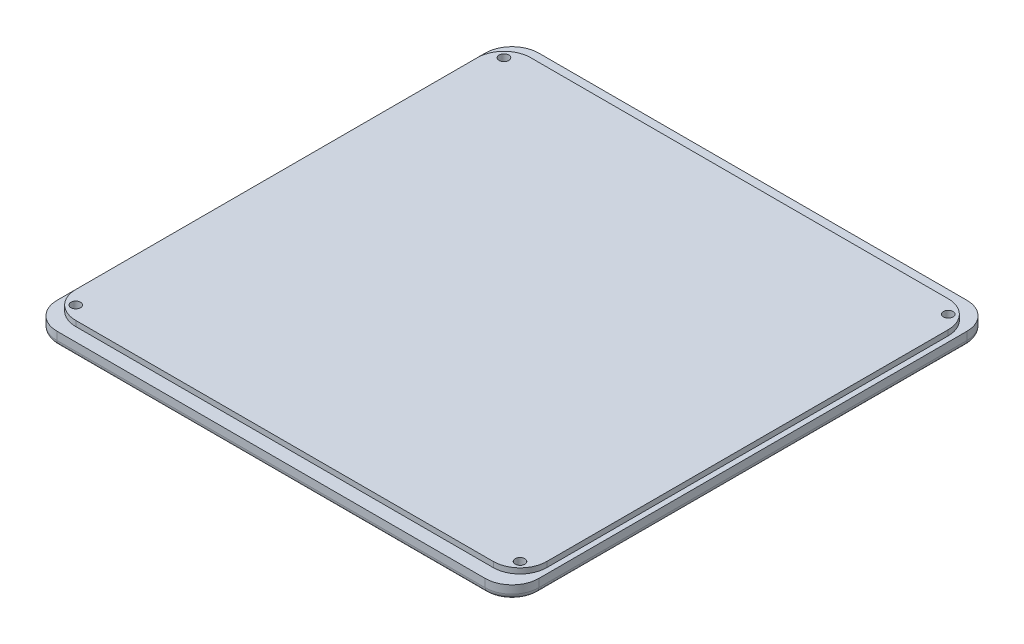
SolidWorks part; units mm, degrees
material "Allzweck-PBT"
ref_plane "Ebene vorne" through (0, 0, 0) normal (0, 0, 1) x (1, 0, 0)
ref_plane "Ebene oben" through (0, 0, 0) normal (0, 1, 0) x (1, 0, 0)
ref_plane "Ebene rechts" through (0, 0, 0) normal (1, 0, 0) x (0, 0, -1)
sketch "Skizze1" plane through (0, 0, 0) normal (0, 1, 0) x (1, 0, 0)
  line L1 (90, 90) -> (-90, 90)
  line L2 (90, 90) -> (90, -90)
  line L3 (90, -90) -> (-90, -90)
  line L4 (-90, 90) -> (-90, -90)
  line L5 (90, 90) -> (-90, -90) construction
  line L6 (90, -90) -> (-90, 90) construction
  point P0 (0, 0)
  dimension "D1" = 180
  dimension "D2" = 180
extrude "Aufsatz-Linear austragen1" add sketch "Skizze1" along normal blind 5 contours L4 L3 L2 L1
sketch "Skizze2" plane through (0, 5, 0) normal (0, 1, 0) x (1, 0, 0)
  line L1 (78, 85) -> (-78, 85)
  line L2 (88, 75) -> (88, -75)
  line L3 (78, -85) -> (-78, -85)
  line L4 (-88, 75) -> (-88, -75)
  line L5 (88, 85) -> (-88, -85) construction
  line L6 (88, -85) -> (-88, 85) construction
  arc A0 (-78, -85) -> (-88, -75) centre (-78, -75) cw
  arc A1 (88, -75) -> (78, -85) centre (78, -75) cw
  arc A2 (78, 85) -> (88, 75) centre (78, 75) cw
  arc A3 (-78, 85) -> (-88, 75) centre (-78, 75) ccw
  point P0 (0, 0)
  dimension "D1" = 10
  dimension "176" = 176
  dimension "D2" = 170
extrude "Aufsatz-Linear austragen2" add sketch "Skizze2" along normal blind 2
hole_wizard "Stirnsenkung für M3 Zylinderschraube mit Innensechskant2" positions "Skizze7" profile "Skizze8" counterbore size "M3" standard "DIN"
sketch "Skizze7" plane through (0, 0, 0) normal (0, -1, 0) x (-1, 0, 0)
  line L0 (-78, 85) -> (78, 85) construction
  line L1 (-88, -75) -> (-88, 75) construction
  line L2 (-78, 85) -> (78, 85) construction
  line L3 (88, 75) -> (88, -75) construction
  line L4 (78, -85) -> (-78, -85) construction
  point P0 (-83, 80)
  point P2 (83, 80)
  point P4 (83, -80)
  point P6 (-83, -80)
  dimension "D1" = 5
  dimension "D2" = 5
  dimension "D3" = 5
  dimension "D4" = 5
  dimension "D5" = 5
  dimension "D6" = 5
  dimension "D7" = 5
  dimension "5" = 5
sketch "Skizze8" plane through (83, 0, -80) normal (1, 0, 0) x (0, 0, -1)
  line L0 (0, 0) -> (0, 10.1815)
  line L1 (0, 10.1815) -> (1.8, 9.1)
  line L2 (1.8, 9.1) -> (1.8, 3.4)
  line L3 (1.8, 3.4) -> (3.25, 3.4)
  line L4 (3.25, 3.4) -> (3.25, 0)
  line L5 (3.25, 0) -> (0, 0)
  line L10 (0, 10.1815) -> (-1.8, 9.1) construction
  line L11 (0, -6.35) -> (0, 107.95) construction
  dimension "Bohrerdurchmesser" = 3.6
  dimension "Bohrungstiefe" = 9.1
  dimension "Senkdurchmesser2" = 6.5
  dimension "Senktiefe2" = 3.4
  dimension "Spitzenwinkel" = 118
fillet "Verrundung1" radius 10 4 edges at (90, 2.5, -90) (90, 2.5, 90) (-90, 2.5, 90) (-90, 2.5, -90)
fillet "Verrundung2" radius 2 8 edges at (87.0711, 0, -87.0711) (0, 0, -90) (-87.0711, 0, -87.0711) (-90, 0, 0) (-87.0711, 0, 87.0711) (0, 0, 90) (87.0711, 0, 87.0711) (90, 0, 0)
